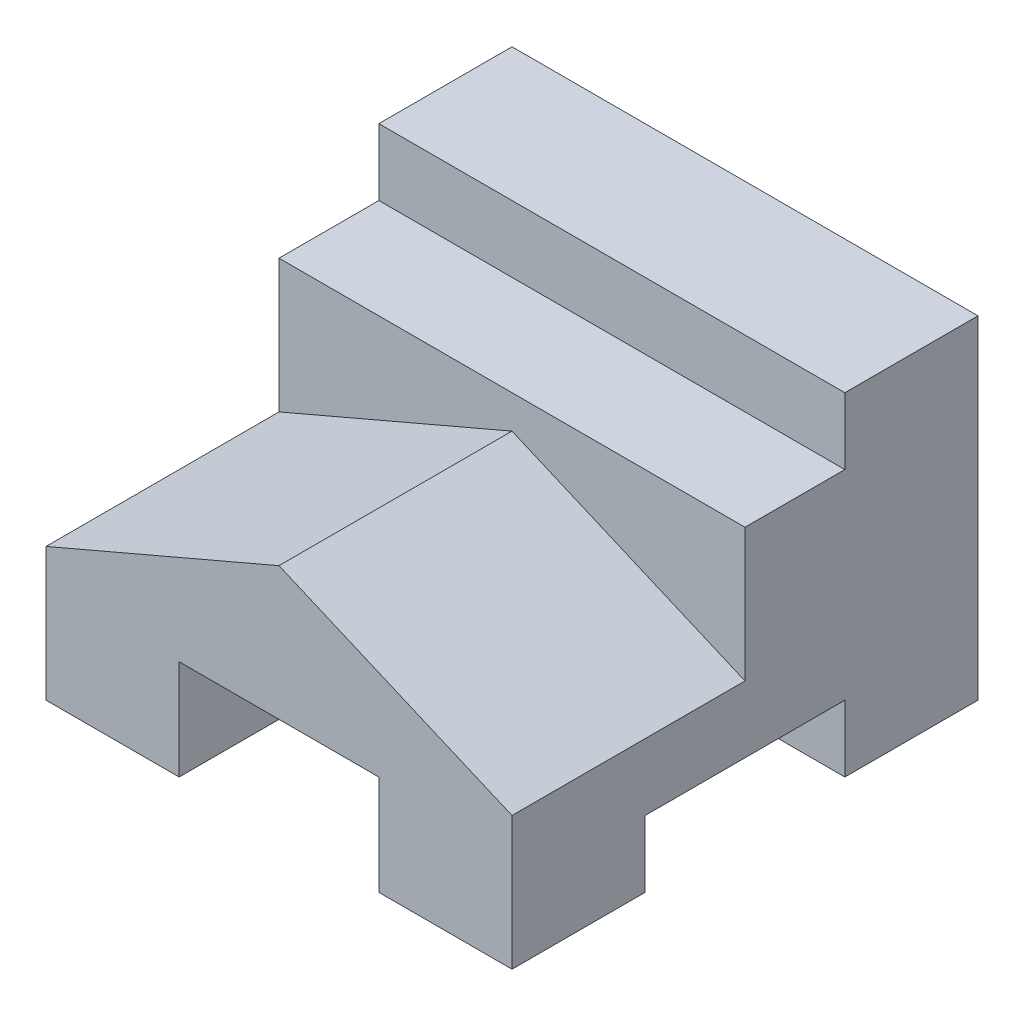
SolidWorks part; units mm, degrees
ref_plane "Ön Düzlem" through (0, 0, 0) normal (0, 0, 1) x (1, 0, 0)
ref_plane "Üst Düzlem" through (0, 0, 0) normal (0, 1, 0) x (1, 0, 0)
ref_plane "Sağ Düzlem" through (0, 0, 0) normal (1, 0, 0) x (0, 0, -1)
sketch "Çizim1" plane through (0, 0, 0) normal (0, 0, 1) x (1, 0, 0)
  line L1 (-31.8773, 27.6908) -> (38.1227, 27.6908)
  line L2 (-31.8773, 27.6908) -> (-31.8773, -22.3092)
  line L3 (-31.8773, -22.3092) -> (38.1227, -22.3092)
  line L4 (38.1227, 27.6908) -> (38.1227, -22.3092)
  dimension "D1" = 70
  dimension "D2" = 50
extrude "Yükseklik-Ekstrüzyon2" add sketch "Çizim1" along normal blind 70
sketch "Çizim2" plane through (-31.8773, 0, 0) normal (-1, 0, 0) x (0, 0, 1)
  line L1 (20, -22.3092) -> (20, -12.3092)
  line L2 (20, -12.3092) -> (50, -12.3092)
  line L3 (50, -12.3092) -> (50, -22.3092)
  line L4 (50, -22.3092) -> (20, -22.3092)
  dimension "D1" = 10
  dimension "D2" = 30
extrude "Kes-Ekstrüzyon1" cut sketch "Çizim2" against normal blind 70
sketch "Çizim7" plane through (0, 0, 70) normal (0, 0, 1) x (1, 0, 0)
  line L1 (-11.8773, -22.3092) -> (-11.8773, -7.3092)
  line L2 (-11.8773, -7.3092) -> (18.1227, -7.3092)
  line L3 (18.1227, -7.3092) -> (18.1227, -22.3092)
  line L4 (18.1227, -22.3092) -> (-11.8773, -22.3092)
  dimension "D1" = 15
extrude "Kes-Ekstrüzyon3" cut sketch "Çizim7" against normal blind 70
sketch "Çizim8" plane through (0, 0, 70) normal (0, 0, 1) x (1, 0, 0)
  line L0 (38.1227, -2.3092) -> (3.1227, 12.6908)
  line L1 (3.1227, 12.6908) -> (-31.8773, -2.3092)
  line L2 (-31.8773, 27.6908) -> (-31.8773, -22.3092) construction
  line L3 (-31.8773, -2.3092) -> (-31.8773, 27.6908)
  line L4 (-31.8773, 27.6908) -> (38.1227, 27.6908)
  line L5 (38.1227, 27.6908) -> (38.1227, -2.3092)
extrude "Kes-Ekstrüzyon4" cut sketch "Çizim8" against normal blind 35
sketch "Çizim9" plane through (-31.8773, 0, 0) normal (-1, 0, 0) x (0, 0, 1)
  line L0 (35, 27.6908) -> (35, 17.6908)
  line L1 (35, 17.6908) -> (20, 17.6908)
  line L2 (20, 17.6908) -> (20, 27.6908)
  line L3 (20, 27.6908) -> (35, 27.6908)
extrude "Kes-Ekstrüzyon5" cut sketch "Çizim9" against normal blind 70
